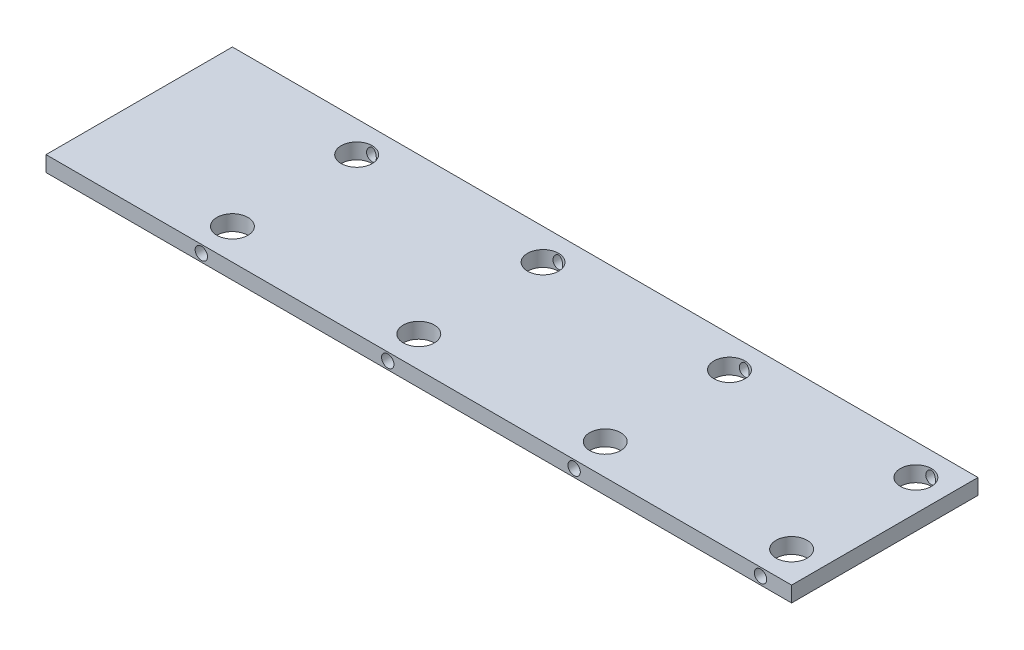
SolidWorks part; units mm, degrees
ref_plane "Front Plane" through (0, 0, 0) normal (0, 0, 1) x (1, 0, 0)
ref_plane "Top Plane" through (0, 0, 0) normal (0, 1, 0) x (1, 0, 0)
ref_plane "Right Plane" through (0, 0, 0) normal (1, 0, 0) x (0, 0, -1)
sketch "Sketch1" plane through (0, 0, 0) normal (0, 0, 1) x (1, 0, 0)
  line L1 (-73.2384, 33.2451) -> (231.5616, 33.2451)
  line L2 (-73.2384, 33.2451) -> (-73.2384, 26.8951)
  line L3 (-73.2384, 26.8951) -> (231.5616, 26.8951)
  line L4 (231.5616, 33.2451) -> (231.5616, 26.8951)
  dimension "D1" = 304.8
  dimension "D2" = 6.35
extrude "Boss-Extrude1" add sketch "Sketch1" along normal blind 76.2
hole_wizard "#8 (0.199) Diameter Hole1" positions "Sketch3" profile "Sketch2" hole size "#8" standard "Ansi Inch"
sketch "Sketch3" plane through (0, 0, 76.2) normal (0, 0, 1) x (1, 0, 0)
  line L0 (-73.2384, 26.8951) -> (231.5616, 26.8951) construction
  line L1 (231.5616, 26.8951) -> (231.5616, 33.2451) construction
  point P0 (218.8616, 30.0701)
  dimension "D1" = 3.175
  dimension "D2" = 12.7
sketch "Sketch2" plane through (218.8616, 30.0701, 76.2) normal (1, 0, 0) x (0, -1, 0)
  line L0 (0, 0) -> (0, 7.8686)
  line L1 (0, 7.8686) -> (2.5273, 6.35)
  line L2 (2.5273, 6.35) -> (2.5273, 0)
  line L5 (2.5273, 0) -> (0, 0)
  line L10 (0, 7.8686) -> (-2.5273, 6.35) construction
  line L11 (0, -6.35) -> (0, 107.95) construction
  dimension "Hole Dia." = 5.0546
  dimension "Hole Depth" = 6.35
  dimension "Drill Angle" = 118
pattern_linear "LPattern1" count 4 spacing 76.2 along (-1, 0, 0) of "#8 (0.199) Diameter Hole1"
sketch "Sketch4" plane through (0, 33.2451, 0) normal (0, 1, 0) x (1, 0, 0)
  line L0 (231.5616, -76.2) -> (231.5616, 0) construction
  line L1 (231.5616, -76.2) -> (-73.2384, -76.2) construction
  circle A0 centre (218.8616, -63.5) radius 6.35
  dimension "D1" = 12.7
  dimension "D2" = 12.7
  dimension "D3" = 12.7
extrude "Cut-Extrude1" cut sketch "Sketch4" against normal through all
pattern_linear "LPattern2" count 4 spacing 76.2 along (-1, 0, 0) count 2 spacing 50.8 along (0, 0, -1) of "Cut-Extrude1"
ref_plane "Plane1" through (0, 0, 38.1) normal (0, 0, 1) x (1, 0, 0)
mirror "Mirror1" about plane through (0, 0, 38.1) normal (0, 0, 1) of "#8 (0.199) Diameter Hole1"
pattern_linear "LPattern3" count 4 spacing 76.2 along (-1, 0, 0) of "Mirror1"
